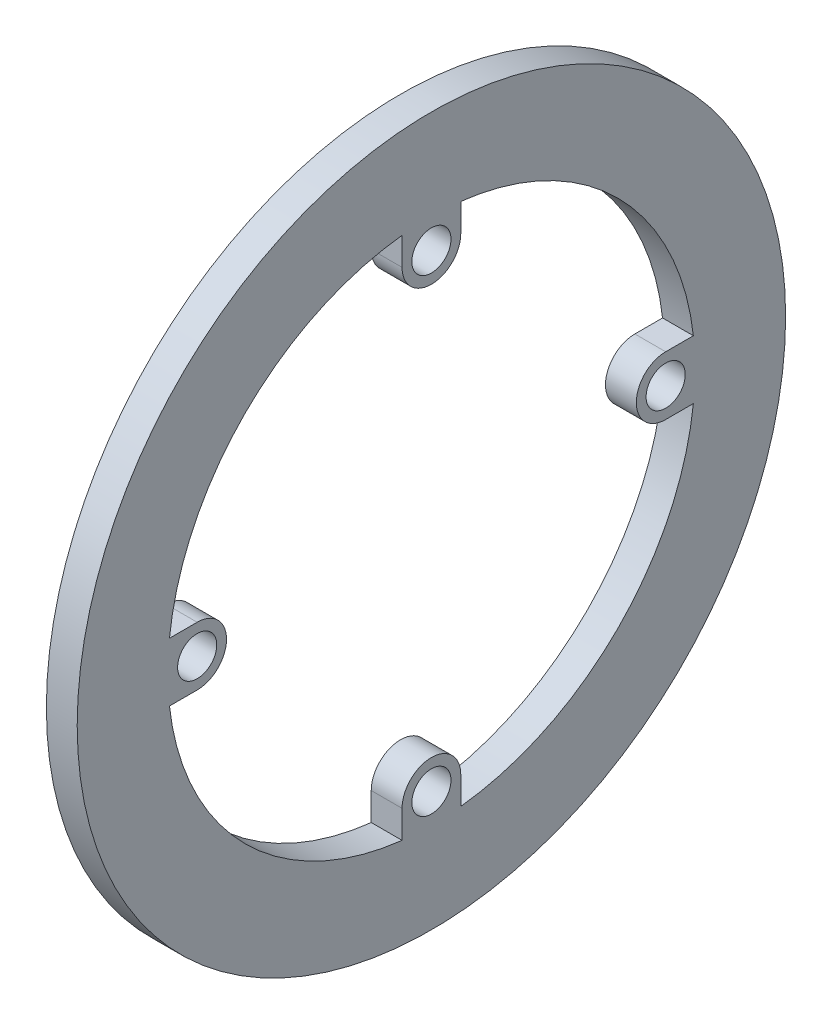
SolidWorks part; units mm, degrees
ref_plane "Front Plane" through (0, 0, 0) normal (0, 0, 1) x (1, 0, 0)
ref_plane "Top Plane" through (0, 0, 0) normal (0, 1, 0) x (1, 0, 0)
ref_plane "Right Plane" through (0, 0, 0) normal (1, 0, 0) x (0, 0, -1)
sketch "Sketch1" plane through (0, 0, 0) normal (1, 0, 0) x (0, 0, -1)
  line L0 (-60.638, 0) -> (60.638, 0) construction
  line L1 (0, -60.638) -> (0, 60.638) construction
  line L2 (-42.4965, 4.7625) -> (-38, 4.7625)
  line L3 (-42.4965, -4.7625) -> (-38, -4.7625)
  line L4 (-4.7625, 42.4965) -> (-4.7625, 38)
  line L5 (4.7625, 42.4965) -> (4.7625, 38)
  line L6 (42.4965, 4.7625) -> (38, 4.7625)
  line L7 (42.4965, -4.7625) -> (38, -4.7625)
  line L8 (4.7625, -42.4965) -> (4.7625, -38)
  line L9 (-4.7625, -42.4965) -> (-4.7625, -38)
  line L10 (0, -41.175) -> (0, -42.7625) construction
  line L11 (0, -33.2375) -> (0, -34.825) construction
  circle A0 centre (0, 0) radius 42.7625
  circle A1 centre (0, 0) radius 57.463
  circle A2 centre (0, 0) radius 60.638 construction
  circle A3 centre (0, 0) radius 38 construction
  circle A4 centre (0, 38) radius 3.175
  circle A5 centre (0, -38) radius 3.175
  circle A6 centre (38, 0) radius 3.175
  circle A7 centre (-38, 0) radius 3.175
  arc A8 (-38, 4.7625) -> (-38, -4.7625) centre (-38, 0) cw
  arc A9 (-4.7625, 38) -> (4.7625, 38) centre (0, 38) ccw
  arc A10 (38, 4.7625) -> (38, -4.7625) centre (38, 0) ccw
  arc A11 (-4.7625, -38) -> (4.7625, -38) centre (0, -38) cw
  dimension "D1" = 121.2761
  dimension "D2" = 76
  dimension "D3" = 6.35
  dimension "D4" = 3.175
  dimension "D5" = 1.5875
extrude "Boss-Extrude1" add sketch "Sketch1" along normal mid plane 5 contours A1 A0 | A8 L2 A0 L3 A7 | L4 A9 L5 A0 A4 | L6 A10 L7 A0 A6 | A11 L9 A0 L8 A5
